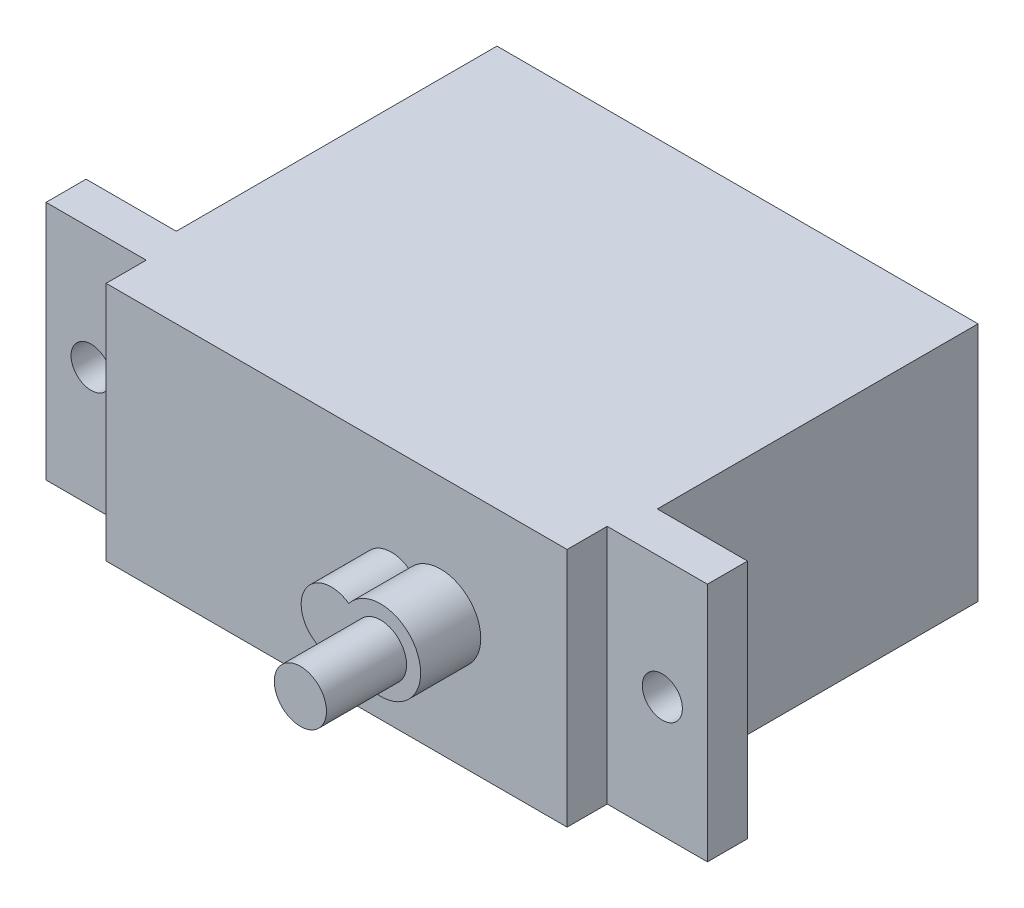
SolidWorks part; units mm, degrees
ref_plane "Front" through (0, 0, 0) normal (0, 0, 1) x (1, 0, 0)
ref_plane "Top" through (0, 0, 0) normal (0, 1, 0) x (1, 0, 0)
ref_plane "Right" through (0, 0, 0) normal (1, 0, 0) x (0, 0, -1)
sketch "草图1" plane through (0, 0, 0) normal (0, 1, 0) x (1, 0, 0)
  line L1 (-12, 8) -> (12, 8)
  line L2 (-12, 8) -> (-12, -8)
  line L3 (-12, -8) -> (12, -8)
  line L4 (12, 8) -> (12, -8)
  line L5 (-12, 8) -> (12, -8) construction
  line L6 (-12, -8) -> (12, 8) construction
  point P0 (0, 0)
  dimension "D1" = 24
  dimension "D2" = 16
extrude "凸台-拉伸1" add sketch "草图1" along normal blind 12
sketch "草图2" plane through (0, 0, 8) normal (0, 0, 1) x (1, 0, 0)
  line L1 (-16.5, 12) -> (16.5, 12)
  line L2 (-16.5, 12) -> (-16.5, 0)
  line L3 (-16.5, 0) -> (16.5, 0)
  line L4 (16.5, 12) -> (16.5, 0)
  line L5 (-16.5, 12) -> (16.5, 0) construction
  line L6 (-16.5, 0) -> (16.5, 12) construction
  point P0 (0, 6)
  dimension "D1" = 33
extrude "凸台-拉伸2" add sketch "草图2" along normal blind 2
sketch "草图3" plane through (0, 0, 8) normal (0, 0, -1) x (-1, 0, 0)
  line L0 (0, 9.8547) -> (0, 1.4014) construction
  line L1 (12, 12) -> (16.5, 12) construction
  circle A0 centre (14.25, 6) radius 1
  circle A1 centre (-14.25, 6) radius 1
  point P9 (14.25, 12)
extrude "切除-拉伸1" cut sketch "草图3" against normal blind 2
sketch "草图4" plane through (0, 0, 10) normal (0, 0, 1) x (1, 0, 0)
  line L0 (-16.5, 0) -> (16.5, 0) construction
  line L1 (-11.5, 12) -> (11.5, 12)
  line L2 (-11.5, 12) -> (-11.5, 0)
  line L3 (-11.5, 0) -> (11.5, 0)
  line L4 (11.5, 12) -> (11.5, 0)
  line L5 (-11.5, 12) -> (11.5, 0) construction
  line L6 (-11.5, 0) -> (11.5, 12) construction
  point P0 (0, 6)
  dimension "D1" = 23
extrude "凸台-拉伸3" add sketch "草图4" along normal blind 2
sketch "草图6" plane through (0, 0, 12) normal (0, 0, 1) x (1, 0, 0)
  arc A0 (3.6058, 4.7816) -> (3.6058, 7.2184) centre (5.1918, 6) ccw
  arc A1 (3.6058, 7.2184) -> (3.6058, 4.7816) centre (2.7308, 6) ccw
  dimension "D1" = 4
  dimension "D2" = 3
extrude "凸台-拉伸4" add sketch "草图6" along normal blind 3
sketch "草图7" plane through (0, 0, 15) normal (0, 0, 1) x (1, 0, 0)
  circle A0 centre (5.1918, 6) radius 1.3
extrude "凸台-拉伸5" add sketch "草图7" along normal blind 4
